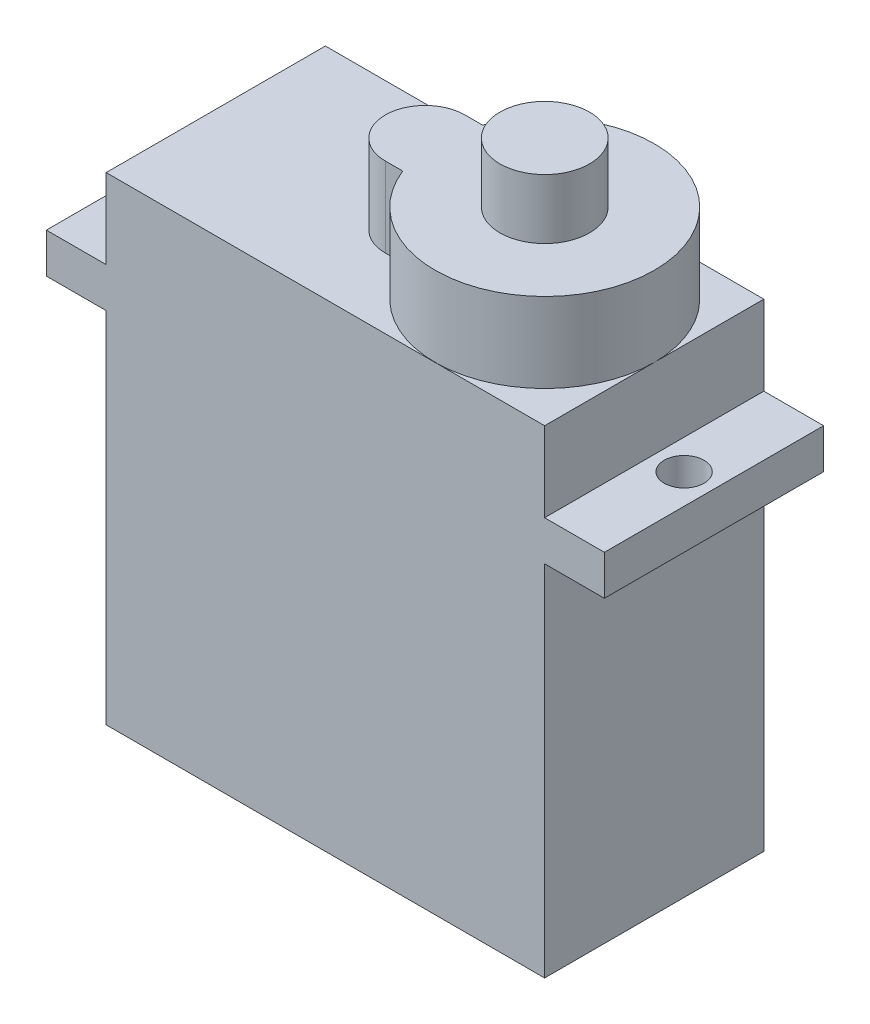
SolidWorks part; units mm, degrees
ref_plane "Front Plane" through (0, 0, 0) normal (0, 0, 1) x (1, 0, 0)
ref_plane "Top Plane" through (0, 0, 0) normal (0, 1, 0) x (1, 0, 0)
ref_plane "Right Plane" through (0, 0, 0) normal (1, 0, 0) x (0, 0, -1)
sketch "Sketch1" plane through (0, 0, 0) normal (0, 1, 0) x (1, 0, 0)
  line L1 (-11, -5.5) -> (11, -5.5)
  line L2 (-11, -5.5) -> (-11, 5.5)
  line L3 (-11, 5.5) -> (11, 5.5)
  line L4 (11, -5.5) -> (11, 5.5)
  line L5 (-11, -5.5) -> (11, 5.5) construction
  line L6 (-11, 5.5) -> (11, -5.5) construction
  point P0 (0, 0)
  dimension "D1" = 22
  dimension "D2" = 11
extrude "Boss-Extrude1" add sketch "Sketch1" along normal blind 24
sketch "Sketch2" plane through (0, 24, 0) normal (0, 1, 0) x (1, 0, 0)
  line L0 (11, -5.5) -> (11, 5.5) construction
  line L1 (-0.5, 2.0065) -> (0.3765, 2.0065)
  line L2 (-0.5, -1.9935) -> (0.3765, -1.9935)
  arc A0 (0.3765, -1.9935) -> (0.3765, 2.0065) centre (5.5, 0.0065) ccw
  arc A1 (-0.5, 2.0065) -> (-0.5, -1.9935) centre (-0.5, 0.0065) ccw
  dimension "D2" = 4
  dimension "D1" = 5.5
  dimension "D3" = 6
extrude "Boss-Extrude2" add sketch "Sketch2" along normal blind 4
sketch "Sketch3" plane through (0, 28, 0) normal (0, 1, 0) x (1, 0, 0)
  circle A0 centre (5.5, 0.0065) radius 2.25
  dimension "D1" = 4.5
sketch "Sketch4" plane through (-11, 0, 0) normal (-1, 0, 0) x (0, 0, 1)
  line L0 (5.5, 24) -> (5.5, 0) construction
  line L1 (-5.5, 20) -> (5.5, 20)
  line L2 (-5.5, 20) -> (-5.5, 18)
  line L3 (-5.5, 18) -> (5.5, 18)
  line L4 (5.5, 20) -> (5.5, 18)
  line L5 (-5.5, 20) -> (5.5, 18) construction
  line L6 (-5.5, 18) -> (5.5, 20) construction
  line L7 (-5.5, 24) -> (5.5, 24) construction
  point P0 (0, 19)
  dimension "D1" = 4
  dimension "D2" = 2
extrude "Boss-Extrude3" add sketch "Sketch4" along normal blind 3
sketch "Sketch5" plane through (0, 20, 0) normal (0, 1, 0) x (1, 0, 0)
  circle A0 centre (-12.5, 0) radius 1
  dimension "D1" = 2
extrude "Cut-Extrude2" cut sketch "Sketch5" against normal through all
mirror "Mirror1" about plane through (0, 0, 0) normal (1, 0, 0) of "Boss-Extrude3", "Cut-Extrude2"
extrude "Boss-Extrude4" add sketch "Sketch3" along normal blind 3
